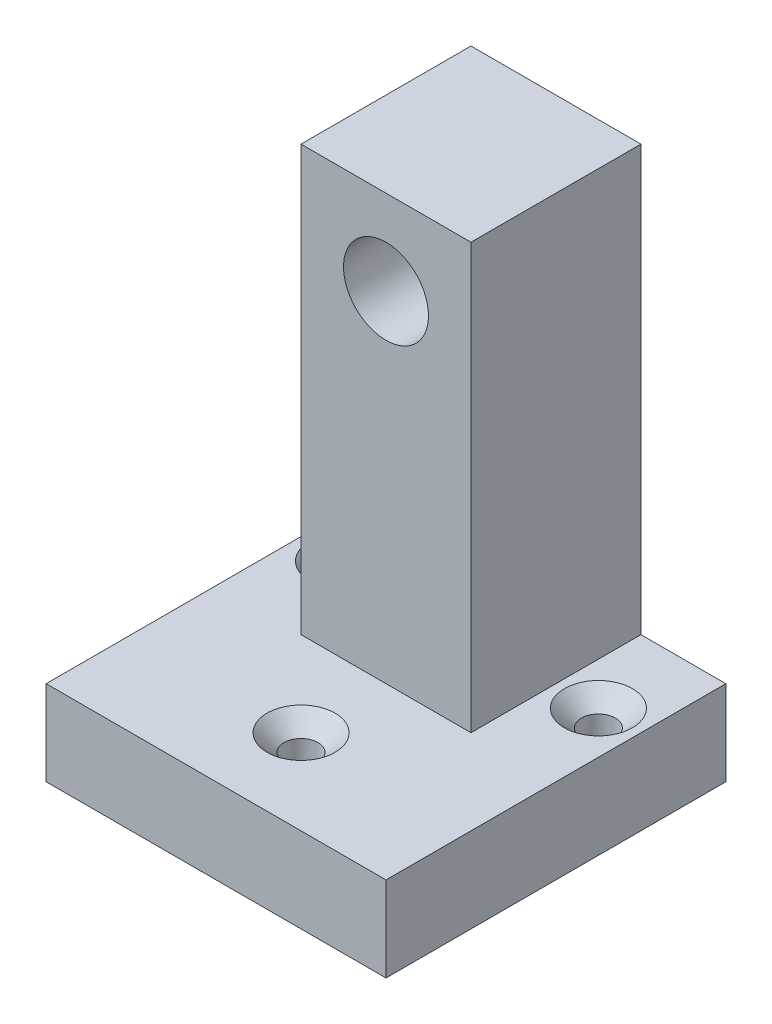
SolidWorks part; units mm, degrees
ref_plane "Plan de face" through (0, 0, 0) normal (0, 0, 1) x (1, 0, 0)
ref_plane "Plan de dessus" through (0, 0, 0) normal (0, 1, 0) x (1, 0, 0)
ref_plane "Plan de droite" through (0, 0, 0) normal (1, 0, 0) x (0, 0, -1)
sketch "Esquisse1" plane through (0, 0, 0) normal (0, 0, 1) x (1, 0, 0)
  line L0 (-4.9542, 0) -> (-0.9542, 0)
  line L1 (-0.9542, 0) -> (-0.9542, 1)
  line L2 (-0.9542, 1) -> (-1.9542, 1)
  line L3 (-1.9542, 1) -> (-1.9542, 6)
  line L4 (-1.9542, 6) -> (-3.9542, 6)
  line L5 (-3.9542, 6) -> (-3.9542, 1)
  line L6 (-3.9542, 1) -> (-4.9542, 1)
  line L7 (-4.9542, 1) -> (-4.9542, 0)
  dimension "D1" = 5
  dimension "D2" = 1
  dimension "D3" = 1
  dimension "D4" = 1
  dimension "D5" = 2
  dimension "D6" = 1
extrude "Boss.-Extru.2" add sketch "Esquisse1" along normal blind 2 contours L5 L6 L7 L0 L1 L2 L3 L4
sketch "Esquisse3" plane through (0, 0, 2) normal (0, 0, 1) x (1, 0, 0)
  line L0 (-3.9542, 1) -> (-1.9542, 1)
  line L1 (-1.9542, 1) -> (-0.9542, 1)
  line L2 (-0.9542, 1) -> (-0.9542, 0)
  line L3 (-0.9542, 0) -> (-4.9542, 0)
  line L4 (-4.9542, 0) -> (-4.9542, 1)
  line L5 (-4.9542, 1) -> (-3.9542, 1)
extrude "Boss.-Extru.3" add sketch "Esquisse3" along normal blind 2
sketch "Esquisse4" plane through (0, 0, 2) normal (0, 0, 1) x (1, 0, 0)
  line L0 (-3.9542, 6) -> (-3.9542, 1) construction
  line L2 (-1.9542, 6) -> (-3.9542, 6) construction
  circle A0 centre (-2.9542, 5) radius 0.5
  point P6 (-5.6767, 3.9197)
  dimension "D1" = 1
  dimension "D2" = 1
  dimension "D3" = 1
extrude "Enlèv. mat.-Extru.1" cut sketch "Esquisse4" against normal blind 2
sketch "Esquisse5" plane through (-3.9542, 0, 0) normal (-1, 0, 0) x (0, 0, 1)
  line L0 (2, 6) -> (2, 1) construction
  line L1 (2, 6) -> (0, 6) construction
  circle A0 centre (1, 5) radius 0.2
  dimension "D1" = 0.4
  dimension "D2" = 1
  dimension "D3" = 1
extrude "Enlèv. mat.-Extru.2" cut sketch "Esquisse5" against normal blind 1
sketch "Esquisse6" plane through (0, 1, 0) normal (0, 1, 0) x (1, 0, 0)
  line L0 (-3.9542, 0) -> (-4.9542, 0) construction
  line L1 (-4.9542, -4) -> (-4.9542, 0) construction
  line L2 (-0.9542, 0) -> (-1.9542, 0) construction
  line L3 (-0.9542, -4) -> (-0.9542, 0) construction
  line L4 (-0.9542, -4) -> (-4.9542, -4) construction
  circle A0 centre (-4.4542, -1) radius 0.2
  circle A1 centre (-1.4542, -1) radius 0.2
  circle A2 centre (-2.9542, -3) radius 0.2
  dimension "D1" = 0.4
  dimension "D2" = 0.4
  dimension "D3" = 0.4
  dimension "D4" = 1
  dimension "D5" = 0.5
  dimension "D6" = 1
  dimension "D7" = 0.5
  dimension "D8" = 1
  dimension "D9" = 2
extrude "Enlèv. mat.-Extru.3" cut sketch "Esquisse6" against normal blind 1
chamfer "Chanfrein1" distance 0.2 angle 45 1 edges at (-3.1542, 1, 3)
chamfer "Chanfrein2" distance 0.2 angle 45 1 edges at (-1.6542, 1, 1)
chamfer "Chanfrein3" distance 0.2 angle 45 1 edges at (-4.6542, 1, 1)
